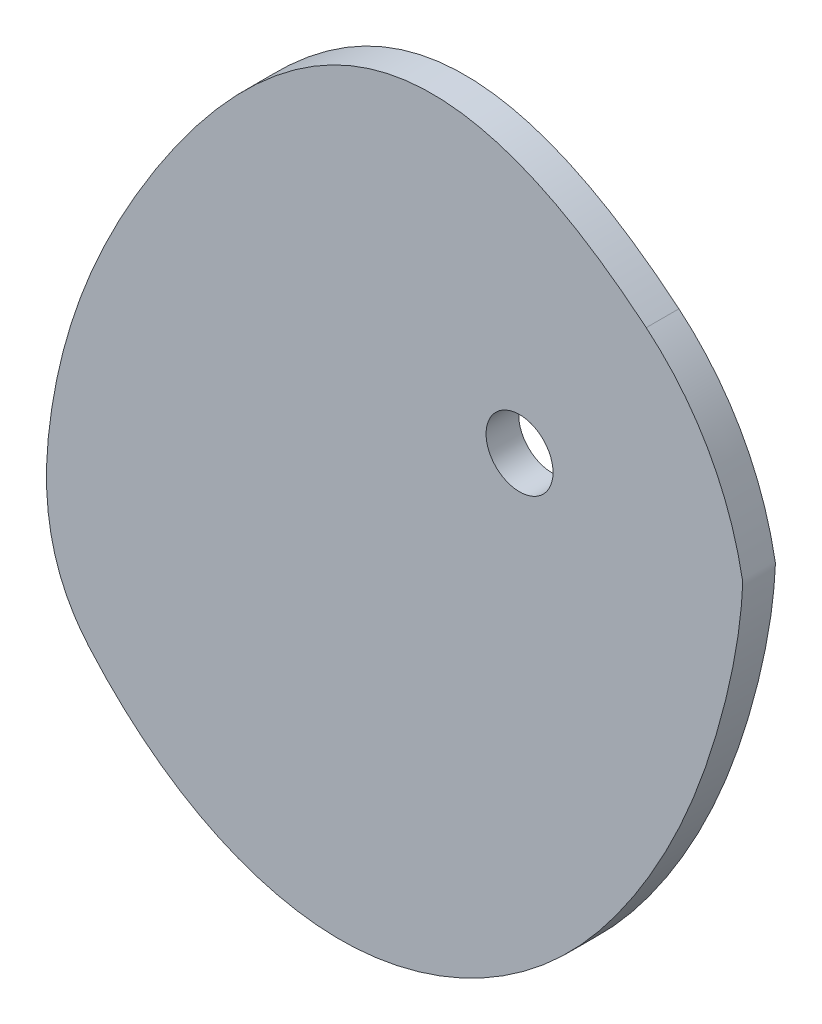
SolidWorks part; units mm, degrees
ref_plane "Front Plane" through (0, 0, 0) normal (0, 0, 1) x (1, 0, 0)
ref_plane "Top Plane" through (0, 0, 0) normal (0, 1, 0) x (1, 0, 0)
ref_plane "Right Plane" through (0, 0, 0) normal (1, 0, 0) x (0, 0, -1)
curve "Curve1"
sketch "Sketch1" plane through (0, 0, 0) normal (0, 0, 1) x (1, 0, 0)
  circle A0 centre (0, 0) radius 3.075
  spline S0 degree 3 poles (11.635, 15.8003) (0.0281, 25.4343) (-17.414, 27.249) (-35.895, 4.2424) (-43.9854, -15.8284) (-43.7845, -30.2734) (-39.5544, -35.1463) knots 0 0 0 0 0.309251 0.582243 0.820017 1 1 1 1
  spline S1 degree 3 number of poles 122 (-39.5544, -35.1463) -> (11.635, 15.8003)
  point P6 (11.635, 15.8003)
  point P8 (0, 0)
  point P10 (-17.2816, 22.2417)
  point P12 (-43.0121, -18.2547)
  dimension "D1" = 6.15
extrude "Boss-Extrude1" add sketch "Sketch1" along normal mid plane 3
sketch "Sketch4" [suppressed] plane through (0, 0, 1.5) normal (0, 0, 1) x (1, 0, 0)
  line L0 (17.5773, -21.2942) -> (-0.4059, -51.7692) construction
  line L1 (-48.8051, -15.5697) -> (-20.0826, 24.9009) construction
  circle A0 centre (-13.2083, -15.9321) radius 29.2387 construction
  spline S0 degree 3 number of poles 363 (20.4693, 0) -> (20.4693, 0) construction
  point P5 (-13.488, -5.936)
  point P6 (-3.3675, -25.0764)
  point P11 (-25.0038, -24.2708)
  point P12 (-13.9531, -18.4277)
  dimension "D1" = 3
  dimension "D2" = 10
hole_wizard "M4 Clearance Hole1" [suppressed] positions "Sketch5" profile "Sketch7" hole size "M4" standard "ANSI Metric"
sketch "Sketch5" [suppressed] plane through (0, 0, 1.5) normal (0, 0, 1) x (1, 0, 0)
  point P0 (-13.488, -5.936)
  point P3 (-3.3675, -25.0764)
  point P6 (-25.0038, -24.2708)
sketch "Sketch7" plane through (-13.488, -5.936, 1.5) normal (1, 0, 0) x (0, -1, 0)
  line L0 (0, 0) -> (0, 3)
  line L1 (0, 3) -> (2.15, 3)
  line L2 (2.15, 3) -> (2.15, 0)
  line L5 (2.15, 0) -> (0, 0)
  line L11 (0, -6.35) -> (0, 107.95) construction
  dimension "Thru Hole Dia." = 4.3
  dimension "Thru Hole Depth" = 3
sketch "Sketch8" plane through (0, 0, 1.5) normal (0, 0, 1) x (1, 0, 0)
  line L5 (-11.09, -40.8947) -> (-20.9198, -47.7776) construction
  line L8 (-28.4462, -45.3019) -> (-27.0696, -47.2679)
  line L9 (-15.2394, -42.4024) -> (-16.8454, -40.1088)
  line L10 (-16.8454, -40.1088) -> (-27.0696, -47.2679)
  line L11 (-6.9178, -29.0068) -> (-3.3617, -34.0855) construction
  line L13 (-6.9178, -29.0068) -> (-18.7955, -37.3237)
  line L15 (-15.2394, -42.4024) -> (-3.3617, -34.0855)
  line L16 (-18.7955, -37.3237) -> (-18.222, -38.1428)
  line L17 (-18.222, -38.1428) -> (-28.4462, -45.3019)
  line L18 (-6.9178, -29.0068) -> (-6.5083, -28.72)
  line L19 (-6.5083, -28.72) -> (-2.9521, -33.7988)
  line L22 (-3.3617, -34.0855) -> (-2.9521, -33.7988)
  spline S1 degree 3 number of poles 363 (20.4693, 0) -> (20.4693, 0) construction
  dimension "D6" = 2.4
  dimension "D1" = 14.5
  dimension "D2" = 2.8
  dimension "D3" = 12
  dimension "D4" = 0.5
  dimension "D8" = 27
  dimension "D9" = 14.5
  dimension "D10" = 6.2
  dimension "D11" = 1
extrude "Cut-Extrude1" [suppressed] cut sketch "Sketch8" against normal through all both and the other way through all
fillet "Fillet1" [suppressed] radius 10
sketch "Sketch10" [suppressed] plane through (0, 0, 0) normal (0, 0, 1) x (1, 0, 0)
  line L1 (-8.5177, -31.4464) -> (-10.3214, -44.6038) construction
  line L2 (-22.8408, -43.8925) -> (-20.9018, -29.7487) construction
  line L3 (-8.5177, -31.4464) -> (-10.3214, -44.6038)
  line L4 (-22.8408, -43.8925) -> (-20.9018, -29.7487)
  circle A6 centre (-13.0442, -46.0588) radius 1.5
  arc A7 (-10.3214, -44.6038) -> (-7.077, -47.3226) centre (-7.8445, -44.9433) ccw construction
  arc A8 (-8.5177, -31.4464) -> (-20.9018, -29.7487) centre (-14.7098, -30.5976) ccw construction
  arc A9 (-26.388, -45.8122) -> (-22.8408, -43.8925) centre (-25.3176, -43.5529) ccw construction
  arc A10 (-10.3214, -44.6038) -> (-7.077, -47.3226) centre (-7.8445, -44.9433) ccw
  arc A11 (-8.5177, -31.4464) -> (-20.9018, -29.7487) centre (-14.7098, -30.5976) ccw
  arc A12 (-26.388, -45.8122) -> (-22.8408, -43.8925) centre (-25.3176, -43.5529) ccw
  spline S1 degree 3 number of poles 363 (-7.077, -47.3226) -> (-26.388, -45.8122) construction
  spline S2 degree 3 number of poles 213 (-7.077, -47.3226) -> (-26.388, -45.8122)
  spline S4 degree 3 number of poles 165 (-53.4212, -32.1303) -> (-53.4212, -32.1303)
  spline S5 degree 3 number of poles 165 (-53.4212, -32.1303) -> (-53.4212, -32.1303)
  dimension "D2" = 3
  dimension "D3" = 2.5
  dimension "D1" = 10
extrude "Boss-Extrude5" [suppressed] add sketch "Sketch10" along normal mid plane 1.5
sketch "Sketch11" [suppressed] plane through (0, 0, 0) normal (0, 0, 1) x (1, 0, 0)
  point P0 (-7.234, 7.8407)
  point P1 (10.4072, 2.3444)
  point P3 (-3.1732, -10.1851)
hole_wizard "M2x0.4 Tapped Hole1" [suppressed] positions "Sketch12" profile "Sketch13" tap size "M2x0.4" standard "ANSI Metric"
sketch "Sketch12" [suppressed] plane through (0, 0, -1.5) normal (0, 0, -1) x (-1, 0, 0)
  point P0 (7.234, 7.8407)
  point P3 (-10.4072, 2.3444)
  point P6 (3.1732, -10.1851)
sketch "Sketch13" plane through (-7.234, 7.8407, -1.5) normal (1, 0, 0) x (0, 1, 0)
  line L0 (0, 0) -> (0, 3)
  line L1 (0, 3) -> (0.7, 3)
  line L2 (0.7, 3) -> (0.7, 0)
  line L5 (0.7, 0) -> (0, 0)
  line L11 (0, -6.35) -> (0, 107.95) construction
  dimension "Thru Tap Drill Dia." = 1.4
  dimension "Thru Tap Drill Depth" = 3
cosmetic thread "Hole Thread1" [suppressed] parameters "D2"=2
cosmetic thread "Hole Thread2" [suppressed] parameters "D2"=2
cosmetic thread "Hole Thread3" [suppressed] parameters "D2"=2
fillet "Fillet2" [suppressed] radius 1.5
sketch "Sketch14" plane through (0, 0, 1.5) normal (0, 0, 1) x (1, 0, 0)
  circle A0 centre (-12.5246, -41.0492) radius 1.05 construction
  circle A1 centre (0, -39.819) radius 1.05
  dimension "D1" = 2.1
  dimension "D2" = 2.1
extrude "Cut-Extrude2" [suppressed] cut sketch "Sketch14" against normal through all
sketch "Sketch15" [suppressed] plane through (0, 0, 0.75) normal (0, 0, 1) x (1, 0, 0)
  circle A0 centre (-24.2994, -39.0947) radius 1.1
  circle A1 centre (-14.3282, -44.0575) radius 1.1
extrude "Cut-Extrude3" [suppressed] cut sketch "Sketch15" against normal blind 10
sketch "Sketch16" [suppressed] plane through (0, 0, 0.75) normal (0, 0, 1) x (1, 0, 0)
  circle A0 centre (-5.523, -52.2474) radius 1.15
  circle A1 centre (5.4449, -44.5935) radius 1.15
  dimension "D1" = 2.3
  dimension "D2" = 2.3
extrude "Cut-Extrude4" [suppressed] cut sketch "Sketch16" against normal blind 10
fillet "Fillet3" [suppressed] radius 0.4
fillet "Fillet4" [suppressed] radius 1.25
